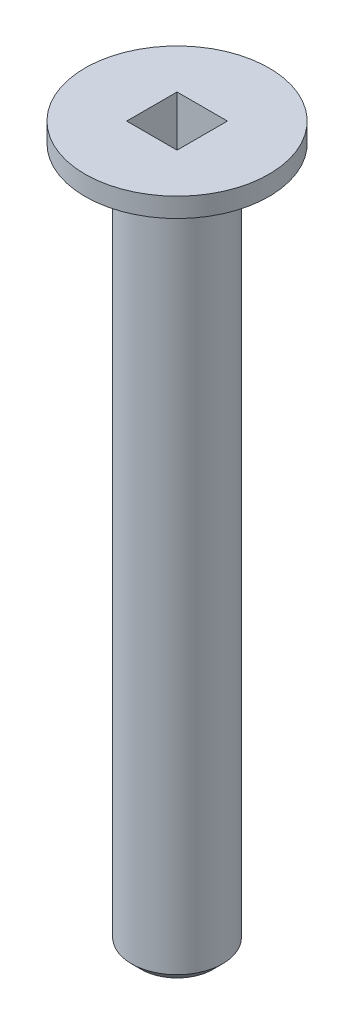
SolidWorks part; units mm, degrees
ref_plane "Front Plane" through (0, 0, 0) normal (0, 0, 1) x (1, 0, 0)
ref_plane "Top Plane" through (0, 0, 0) normal (0, 1, 0) x (1, 0, 0)
ref_plane "Right Plane" through (0, 0, 0) normal (1, 0, 0) x (0, 0, -1)
sketch "Sketch1" plane through (0, 0, 0) normal (0, 1, 0) x (1, 0, 0)
  circle A0 centre (0, 0) radius 2.35
  dimension "D1" = 4.7
extrude "Boss-Extrude1" add sketch "Sketch1" along normal blind 37
sketch "Sketch2" plane through (0, 0, 0) normal (1, 0, 0) x (0, 0, -1)
  line L0 (0, 37) -> (-4.75, 37)
  line L1 (2.35, 37) -> (-2.35, 37) construction
  line L2 (-4.75, 37) -> (-4.75, 36)
  line L3 (-4.75, 36) -> (0, 33)
  line L4 (0, 33) -> (0, 37)
  line L5 (0, 33) -> (0, 0) construction
  dimension "D1" = 4.75
  dimension "D2" = 1
  dimension "D3" = 4
revolve "Revolve1" add sketch "Sketch2" angle 360 about L5
chamfer "Chamfer1" distance 0.5 angle 45 1 edges at (0, 0, 2.35)
sketch "Sketch3" plane through (0, 37, 0) normal (0, 1, 0) x (1, 0, 0)
  line L1 (1.3, 1.3) -> (-1.3, 1.3)
  line L2 (1.3, 1.3) -> (1.3, -1.3)
  line L3 (1.3, -1.3) -> (-1.3, -1.3)
  line L4 (-1.3, 1.3) -> (-1.3, -1.3)
  line L5 (1.3, 1.3) -> (-1.3, -1.3) construction
  line L6 (1.3, -1.3) -> (-1.3, 1.3) construction
  point P0 (0, 0)
  dimension "D1" = 2.6
extrude "Cut-Extrude1" cut sketch "Sketch3" against normal blind 2.8
